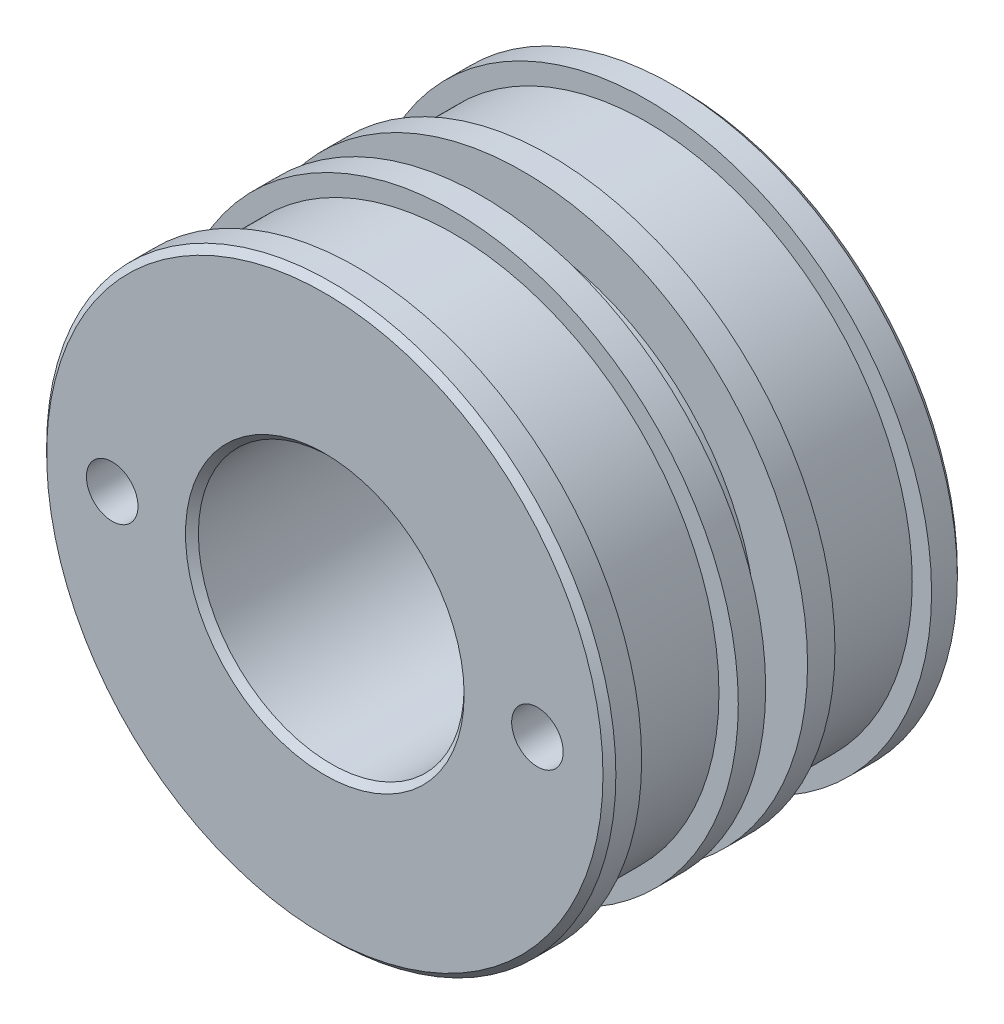
SolidWorks part; units mm, degrees
ref_plane "Front Plane" through (0, 0, 0) normal (0, 0, 1) x (1, 0, 0)
ref_plane "Top Plane" through (0, 0, 0) normal (0, 1, 0) x (1, 0, 0)
ref_plane "Right Plane" through (0, 0, 0) normal (1, 0, 0) x (0, 0, -1)
sketch "Sketch1" plane through (0, 0, 0) normal (0, 0, 1) x (1, 0, 0)
  circle A0 centre (0, 0) radius 44.175
  circle A1 centre (0, 0) radius 20.625
  dimension "D1" = 88.35
  dimension "D2" = 41.25
extrude "Boss-Extrude1" add sketch "Sketch1" against normal blind 55
sketch "Sketch2" plane through (0, 0, 0) normal (1, 0, 0) x (0, 0, -1)
  line L0 (0, 0) -> (63.0016, 0) construction
  line L1 (55, 44.175) -> (0, 44.175) construction
  line L2 (5, 44.175) -> (20, 44.175)
  line L3 (5, 44.175) -> (5, 41.175)
  line L4 (5, 41.175) -> (20, 41.175)
  line L5 (20, 44.175) -> (20, 41.175)
  line L6 (0, 44.175) -> (0, -44.175) construction
  line L11 (50, 44.175) -> (35, 44.175)
  line L12 (50, 44.175) -> (50, 41.175)
  line L13 (50, 41.175) -> (35, 41.175)
  line L14 (35, 44.175) -> (35, 41.175)
  line L15 (24.25, 44.175) -> (30.75, 44.175)
  line L16 (24.25, 44.175) -> (24.25, 36.175)
  line L17 (24.25, 36.175) -> (30.75, 36.175)
  line L18 (30.75, 44.175) -> (30.75, 36.175)
  line L19 (55, -44.175) -> (55, 44.175) construction
  dimension "D1" = 5
  dimension "D2" = 3
  dimension "D3" = 15
  dimension "D4" = 8
  dimension "D5" = 6.5
  dimension "D6" = 4.25
  dimension "D7" = 5
revolve "Cut-Revolve1" cut sketch "Sketch2" angle 360 about L0
chamfer "Chamfer1" distance 1 angle 45 4 edges at (20.625, 0, -55) (44.175, 0, -55) (20.625, 0, 0) (44.175, 0, 0)
sketch "Sketch3" plane through (0, 0, -55) normal (0, 0, -1) x (-1, 0, 0)
  circle A0 centre (0, 0) radius 24.5
  dimension "D1" = 49
extrude "Cut-Extrude1" cut sketch "Sketch3" against normal blind 15
chamfer "Chamfer2" distance 1 angle 45 1 edges at (-24.5, 0, -55)
sketch "Sketch4" plane through (0, 0, 0) normal (0, 0, 1) x (1, 0, 0)
  circle A0 centre (0, 0) radius 33 construction
  circle A1 centre (-33, 0) radius 4
  circle A2 centre (33, 0) radius 4
  dimension "D1" = 8
extrude "Cut-Extrude2" cut sketch "Sketch4" against normal blind 9
